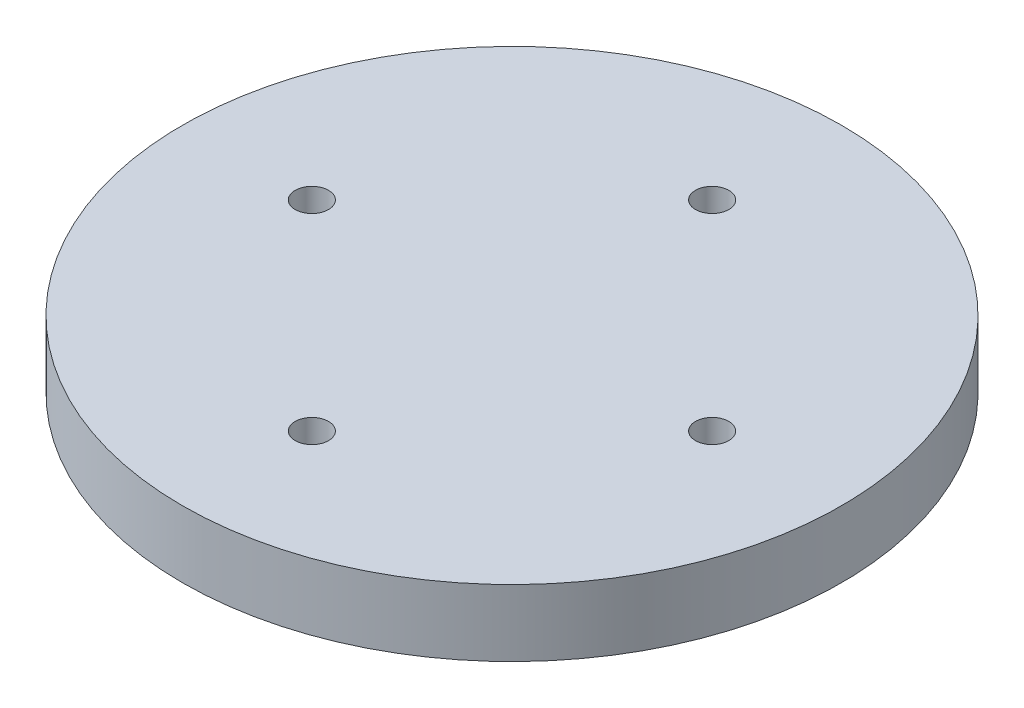
SolidWorks part; units mm, degrees
ref_plane "Front Plane" through (0, 0, 0) normal (0, 0, 1) x (1, 0, 0)
ref_plane "Top Plane" through (0, 0, 0) normal (0, 1, 0) x (1, 0, 0)
ref_plane "Right Plane" through (0, 0, 0) normal (1, 0, 0) x (0, 0, -1)
sketch "Sketch1" plane through (0, 0, 0) normal (0, 1, 0) x (1, 0, 0)
  circle A0 centre (0, 0) radius 62.738
  dimension "D1" = 125.476
extrude "Boss-Extrude1" add sketch "Sketch1" along normal blind 12.7 contours A0
sketch "Sketch2" plane through (0, 12.7, 0) normal (0, 1, 0) x (1, 0, 0)
  line L0 (0, 0) -> (99.6862, 0) construction
  circle A0 centre (38.1, 0) radius 3.175
  circle A1 centre (0, -38.1) radius 3.175
  circle A2 centre (-38.1, 0) radius 3.175
  circle A3 centre (0, 38.1) radius 3.175
  point P14 (0, 0)
  dimension "D1" = 6.35
  dimension "D2" = 4
  dimension "D3" = 38.1
extrude "Cut-Extrude1" cut sketch "Sketch2" against normal blind 6.35
